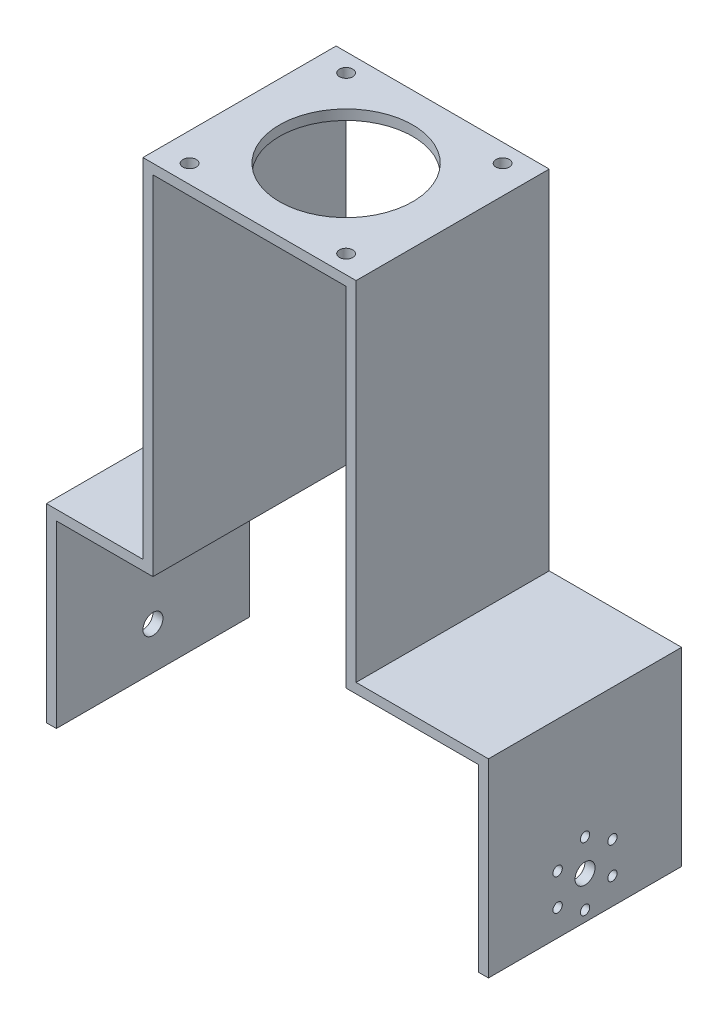
SolidWorks part; units mm, degrees
material "1060 Alloy"
ref_plane "Front Plane" through (0, 0, 0) normal (0, 0, 1) x (1, 0, 0)
ref_plane "Top Plane" through (0, 0, 0) normal (0, 1, 0) x (1, 0, 0)
ref_plane "Right Plane" through (0, 0, 0) normal (1, 0, 0) x (0, 0, -1)
sketch "Sketch2" plane through (0, 0, 0) normal (0, 0, 1) x (1, 0, 0)
  line L0 (0, 51.8967) -> (32, 51.8967)
  line L1 (32, 51.8967) -> (32, -52.6033)
  line L2 (32, -52.6033) -> (71.75, -52.6033)
  line L3 (71.75, -52.6033) -> (71.75, -109.6033)
  line L4 (0, 51.8967) -> (-32, 51.8967)
  line L5 (-32, 51.8967) -> (-32, -52.6033)
  line L6 (-32, -52.6033) -> (-61, -52.6033)
  line L7 (-61, -52.6033) -> (-61, -109.6033)
  line L8 (-58, -55.6033) -> (-58, -109.6033)
  line L9 (-29, -55.6033) -> (-58, -55.6033)
  line L10 (-29, 48.8967) -> (-29, -55.6033)
  line L11 (0, 48.8967) -> (-29, 48.8967)
  line L12 (0, 48.8967) -> (29, 48.8967)
  line L13 (29, 48.8967) -> (29, -55.6033)
  line L14 (29, -55.6033) -> (68.75, -55.6033)
  line L15 (68.75, -55.6033) -> (68.75, -109.6033)
  line L16 (-61, -109.6033) -> (-58, -109.6033)
  line L17 (68.75, -109.6033) -> (71.75, -109.6033)
  dimension "D1" = 32
  dimension "D2" = 104.5
  dimension "D3" = 39.75
  dimension "D4" = 57
  dimension "D5" = 32
  dimension "D6" = 29
  dimension "D7" = 3
extrude "Boss-Extrude1" add sketch "Sketch2" along normal blind 58
sketch "Sketch3" plane through (0, 51.8967, 0) normal (0, 1, 0) x (1, 0, 0)
  line L0 (-32, 0) -> (-23.5, 0) construction
  line L1 (32, 0) -> (-32, 0) construction
  line L2 (-23.5, 0) -> (-23.5, -5.5) construction
  line L3 (-32, -29) -> (32, -29) construction
  line L4 (-32, -58) -> (-32, 0) construction
  line L5 (32, -58) -> (32, 0) construction
  line L6 (0, 0) -> (0, -57.402) construction
  circle A0 centre (-23.5, -5.5) radius 2
  circle A1 centre (23.5, -5.5) radius 2
  circle A2 centre (23.5, -52.5) radius 2
  circle A3 centre (-23.5, -52.5) radius 2
  circle A4 centre (0, -29) radius 20
  dimension "D3" = 4
  dimension "D4" = 40
  dimension "D1" = 8.5
  dimension "D2" = 5.5
  dimension "D5" = 47
extrude "Cut-Extrude1" cut sketch "Sketch3" against normal blind 58
sketch "Sketch4" plane through (71.75, 0, 0) normal (1, 0, 0) x (0, 0, -1)
  line L0 (-58, -109.6033) -> (-58, -96.9033) construction
  line L1 (-58, -109.6033) -> (-58, -52.6033) construction
  line L2 (-58, -96.9033) -> (-29, -96.9033) construction
  circle A0 centre (-29, -96.9033) radius 3
  circle A2 centre (-29, -87.4033) radius 1.4
  circle A3 centre (-20.7728, -92.1533) radius 1.4
  circle A4 centre (-20.7728, -101.6533) radius 1.4
  circle A5 centre (-29, -106.4033) radius 1.4
  circle A6 centre (-37.2272, -101.6533) radius 1.4
  circle A7 centre (-37.2272, -92.1533) radius 1.4
  point P23 (-29, -96.9033)
  dimension "D2" = 6
  dimension "D4" = 2.8
  dimension "D1" = 12.7
  dimension "D5" = 6
extrude "Cut-Extrude2" cut sketch "Sketch4" against normal blind 58
sketch "Sketch5" plane through (-61, 0, 0) normal (-1, 0, 0) x (0, 0, 1)
  line L0 (0, -109.6033) -> (0, -96.9033) construction
  line L1 (0, -52.6033) -> (0, -109.6033) construction
  line L2 (0, -96.9033) -> (29, -96.9033) construction
  circle A0 centre (29, -96.9033) radius 3
  dimension "D2" = 6
  dimension "D1" = 12.7
extrude "Cut-Extrude3" cut sketch "Sketch5" against normal blind 58
